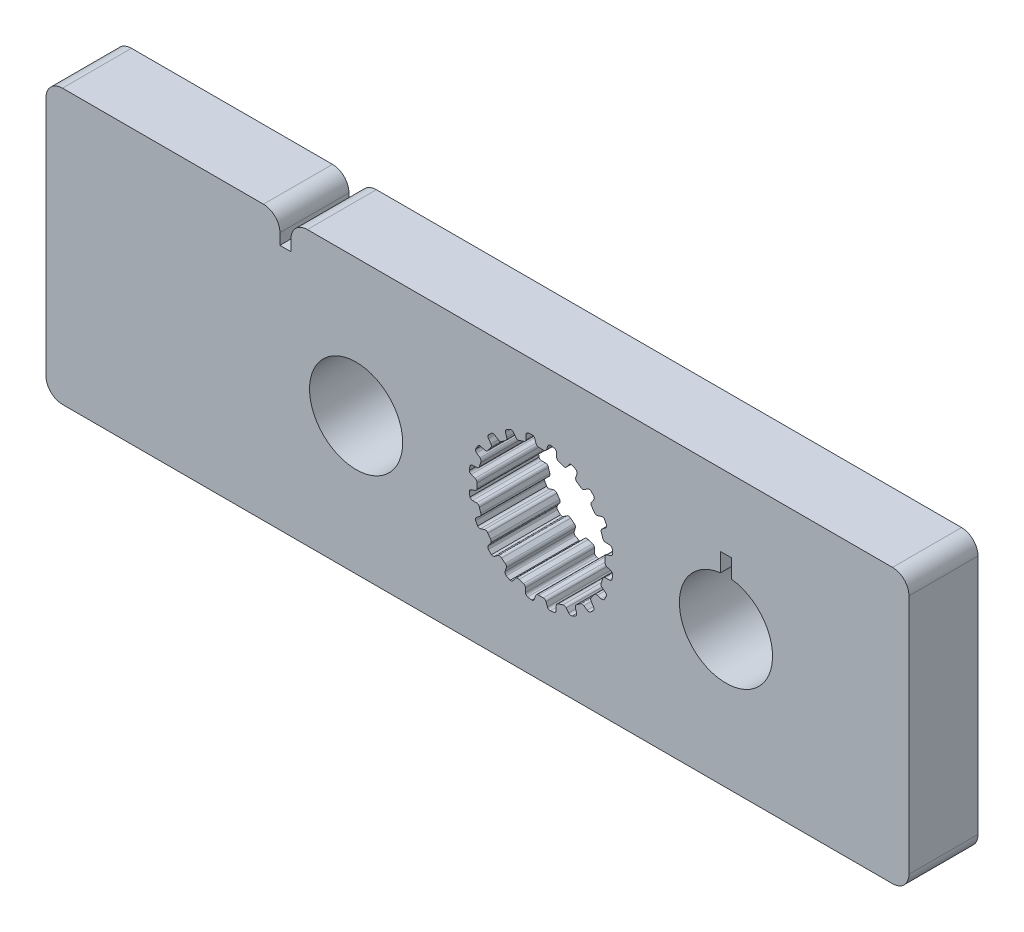
SolidWorks part; units mm, degrees
ref_plane "Front Plane" through (0, 0, 0) normal (0, 0, 1) x (1, 0, 0)
ref_plane "Top Plane" through (0, 0, 0) normal (0, 1, 0) x (1, 0, 0)
ref_plane "Right Plane" through (0, 0, 0) normal (1, 0, 0) x (0, 0, -1)
sketch "Sketch1" plane through (0, 0, 0) normal (0, 0, 1) x (1, 0, 0)
  line L0 (-0.1069, 2.9699) -> (0.1069, 2.9699)
  line L1 (0.3159, 3.2375) -> (0.2537, 3.0575)
  line L2 (-0.2964, 3.2367) -> (-0.2318, 3.0575)
  line L3 (-0.2964, 3.2367) -> (0.3159, 3.2375) construction
  line L4 (0, 3.3252) -> (0, 0) construction
  line L5 (-0.2318, 3.0575) -> (0.2537, 3.0575) construction
  line L6 (-0.4281, 3.3241) -> (0.4281, 3.3263) construction
  line L7 (0.7183, 3.1698) -> (0.7244, 2.9795)
  line L8 (0.816, 2.8576) -> (1.0195, 2.7915)
  line L9 (1.3009, 2.9815) -> (1.1862, 2.8295)
  line L10 (1.6627, 2.7927) -> (1.6097, 2.6099)
  line L11 (1.6591, 2.4655) -> (1.8322, 2.3398)
  line L12 (2.1585, 2.4335) -> (2.0025, 2.3245)
  line L13 (2.4443, 2.1423) -> (2.3374, 1.9847)
  line L14 (2.3398, 1.8322) -> (2.4655, 1.6591)
  line L15 (2.8049, 1.6474) -> (2.6228, 1.5919)
  line L16 (2.9866, 1.2821) -> (2.8363, 1.1653)
  line L17 (2.7915, 1.0195) -> (2.8576, 0.816)
  line L18 (3.1767, 0.7) -> (2.9863, 0.7035)
  line L19 (3.2367, 0.2964) -> (3.0575, 0.2318)
  line L20 (2.9699, 0.1069) -> (2.9699, -0.1069)
  line L21 (3.2375, -0.3159) -> (3.0575, -0.2537)
  line L22 (3.1698, -0.7183) -> (2.9795, -0.7244)
  line L23 (2.8576, -0.816) -> (2.7915, -1.0195)
  line L24 (2.9815, -1.3009) -> (2.8295, -1.1862)
  line L25 (2.7927, -1.6627) -> (2.6099, -1.6097)
  line L26 (2.4655, -1.6591) -> (2.3398, -1.8322)
  line L27 (2.4335, -2.1585) -> (2.3245, -2.0025)
  line L28 (2.1423, -2.4443) -> (1.9847, -2.3374)
  line L29 (1.8322, -2.3398) -> (1.6591, -2.4655)
  line L30 (1.6474, -2.8049) -> (1.5919, -2.6228)
  line L31 (1.2821, -2.9866) -> (1.1653, -2.8363)
  line L32 (1.0195, -2.7915) -> (0.816, -2.8576)
  line L33 (0.7, -3.1767) -> (0.7035, -2.9863)
  line L34 (0.2964, -3.2367) -> (0.2318, -3.0575)
  line L35 (0.1069, -2.9699) -> (-0.1069, -2.9699)
  line L36 (-0.3159, -3.2375) -> (-0.2537, -3.0575)
  line L37 (-0.7183, -3.1698) -> (-0.7244, -2.9795)
  line L38 (-0.816, -2.8576) -> (-1.0195, -2.7915)
  line L39 (-1.3009, -2.9815) -> (-1.1862, -2.8295)
  line L40 (-1.6627, -2.7927) -> (-1.6097, -2.6099)
  line L41 (-1.6591, -2.4655) -> (-1.8322, -2.3398)
  line L42 (-2.1585, -2.4335) -> (-2.0025, -2.3245)
  line L43 (-2.4443, -2.1423) -> (-2.3374, -1.9847)
  line L44 (-2.3398, -1.8322) -> (-2.4655, -1.6591)
  line L45 (-2.8049, -1.6474) -> (-2.6228, -1.5919)
  line L46 (-2.9866, -1.2821) -> (-2.8363, -1.1653)
  line L47 (-2.7915, -1.0195) -> (-2.8576, -0.816)
  line L48 (-3.1767, -0.7) -> (-2.9863, -0.7035)
  line L49 (-3.2367, -0.2964) -> (-3.0575, -0.2318)
  line L50 (-2.9699, -0.1069) -> (-2.9699, 0.1069)
  line L51 (-3.2375, 0.3159) -> (-3.0575, 0.2537)
  line L52 (-3.1698, 0.7183) -> (-2.9795, 0.7244)
  line L53 (-2.8576, 0.816) -> (-2.7915, 1.0195)
  line L54 (-2.9815, 1.3009) -> (-2.8295, 1.1862)
  line L55 (-2.7927, 1.6627) -> (-2.6099, 1.6097)
  line L56 (-2.4655, 1.6591) -> (-2.3398, 1.8322)
  line L57 (-2.4335, 2.1585) -> (-2.3245, 2.0025)
  line L58 (-2.1423, 2.4443) -> (-1.9847, 2.3374)
  line L59 (-1.8322, 2.3398) -> (-1.6591, 2.4655)
  line L60 (-1.6474, 2.8049) -> (-1.5919, 2.6228)
  line L61 (-1.2821, 2.9866) -> (-1.1653, 2.8363)
  line L62 (-1.0195, 2.7915) -> (-0.816, 2.8576)
  line L63 (-0.7, 3.1767) -> (-0.7035, 2.9863)
  line L64 (0.4281, 3.3263) -> (0.62, 3.2938)
  line L65 (1.4351, 3.0312) -> (1.6075, 2.9409)
  line L66 (2.3015, 2.4394) -> (2.4376, 2.3003)
  line L67 (2.9427, 1.6088) -> (3.0291, 1.4344)
  line L68 (3.2958, 0.6207) -> (3.3241, 0.4281)
  line L69 (3.3263, -0.4281) -> (3.2938, -0.62)
  line L70 (3.0312, -1.4351) -> (2.9409, -1.6075)
  line L71 (2.4394, -2.3015) -> (2.3003, -2.4376)
  line L72 (1.6088, -2.9427) -> (1.4344, -3.0291)
  line L73 (0.6207, -3.2958) -> (0.4281, -3.3241)
  line L74 (-0.4281, -3.3263) -> (-0.62, -3.2938)
  line L75 (-1.4351, -3.0312) -> (-1.6075, -2.9409)
  line L76 (-2.3015, -2.4394) -> (-2.4376, -2.3003)
  line L77 (-2.9427, -1.6088) -> (-3.0291, -1.4344)
  line L78 (-3.2958, -0.6207) -> (-3.3241, -0.4281)
  line L79 (-3.3263, 0.4281) -> (-3.2938, 0.62)
  line L80 (-3.0312, 1.4351) -> (-2.9409, 1.6075)
  line L81 (-2.4394, 2.3015) -> (-2.3003, 2.4376)
  line L82 (-1.6088, 2.9427) -> (-1.4344, 3.0291)
  line L83 (-0.6207, 3.2958) -> (-0.4281, 3.3241)
  line L84 (0, 0) -> (0, -6.35) construction
  line L85 (-22.9489, 6.35) -> (17.0561, 6.35)
  line L86 (-22.9489, 6.35) -> (-22.9489, -6.35)
  line L87 (-22.9489, -6.35) -> (17.0561, -6.35)
  line L88 (17.0561, 6.35) -> (17.0561, -6.35)
  line L89 (-8.5725, 0) -> (8.5725, 0) construction
  arc A0 (0.2537, 3.0575) -> (0.1069, 2.9699) centre (0.1283, 3.1009) cw
  arc A1 (-0.2318, 3.0575) -> (-0.1069, 2.9699) centre (-0.1069, 3.1026) ccw
  arc A2 (0.62, 3.2938) -> (0.7183, 3.1698) centre (0.5856, 3.1656) cw
  arc A3 (0.7244, 2.9795) -> (0.816, 2.8576) centre (0.857, 2.9838) ccw
  arc A4 (-0.4281, 3.3241) -> (-0.2964, 3.2367) centre (-0.4213, 3.1916) cw
  arc A5 (0.4281, 3.3263) -> (0.3159, 3.2375) centre (0.4413, 3.1942) ccw
  arc A6 (1.1862, 2.8295) -> (1.0195, 2.7915) centre (1.0802, 2.9095) cw
  arc A7 (1.4351, 3.0312) -> (1.3009, 2.9815) centre (1.4068, 2.9015) ccw
  arc A8 (1.6075, 2.9409) -> (1.6627, 2.7927) centre (1.5352, 2.8297) cw
  arc A9 (1.6097, 2.6099) -> (1.6591, 2.4655) centre (1.7371, 2.5729) ccw
  arc A10 (2.0025, 2.3245) -> (1.8322, 2.3398) centre (1.9264, 2.4332) cw
  arc A11 (2.3015, 2.4394) -> (2.1585, 2.4335) centre (2.2346, 2.3248) ccw
  arc A12 (2.4376, 2.3003) -> (2.4443, 2.1423) centre (2.3345, 2.2168) cw
  arc A13 (2.3374, 1.9847) -> (2.3398, 1.8322) centre (2.4472, 1.9102) ccw
  arc A14 (2.6228, 1.5919) -> (2.4655, 1.6591) centre (2.5841, 1.7189) cw
  arc A15 (2.9427, 1.6088) -> (2.8049, 1.6474) centre (2.8436, 1.5205) ccw
  arc A16 (3.0291, 1.4344) -> (2.9866, 1.2821) centre (2.9052, 1.3869) cw
  arc A17 (2.8363, 1.1653) -> (2.7915, 1.0195) centre (2.9177, 1.0605) ccw
  arc A18 (2.9863, 0.7035) -> (2.8576, 0.816) centre (2.9887, 0.8362) cw
  arc A19 (3.2958, 0.6207) -> (3.1767, 0.7) centre (3.1743, 0.5673) ccw
  arc A20 (3.3241, 0.4281) -> (3.2367, 0.2964) centre (3.1916, 0.4213) cw
  arc A21 (3.0575, 0.2318) -> (2.9699, 0.1069) centre (3.1026, 0.1069) ccw
  arc A22 (3.0575, -0.2537) -> (2.9699, -0.1069) centre (3.1009, -0.1283) cw
  arc A23 (3.3263, -0.4281) -> (3.2375, -0.3159) centre (3.1942, -0.4413) ccw
  arc A24 (3.2938, -0.62) -> (3.1698, -0.7183) centre (3.1656, -0.5856) cw
  arc A25 (2.9795, -0.7244) -> (2.8576, -0.816) centre (2.9838, -0.857) ccw
  arc A26 (2.8295, -1.1862) -> (2.7915, -1.0195) centre (2.9095, -1.0802) cw
  arc A27 (3.0312, -1.4351) -> (2.9815, -1.3009) centre (2.9015, -1.4068) ccw
  arc A28 (2.9409, -1.6075) -> (2.7927, -1.6627) centre (2.8297, -1.5352) cw
  arc A29 (2.6099, -1.6097) -> (2.4655, -1.6591) centre (2.5729, -1.7371) ccw
  arc A30 (2.3245, -2.0025) -> (2.3398, -1.8322) centre (2.4332, -1.9264) cw
  arc A31 (2.4394, -2.3015) -> (2.4335, -2.1585) centre (2.3248, -2.2346) ccw
  arc A32 (2.3003, -2.4376) -> (2.1423, -2.4443) centre (2.2168, -2.3345) cw
  arc A33 (1.9847, -2.3374) -> (1.8322, -2.3398) centre (1.9102, -2.4472) ccw
  arc A34 (1.5919, -2.6228) -> (1.6591, -2.4655) centre (1.7189, -2.5841) cw
  arc A35 (1.6088, -2.9427) -> (1.6474, -2.8049) centre (1.5205, -2.8436) ccw
  arc A36 (1.4344, -3.0291) -> (1.2821, -2.9866) centre (1.3869, -2.9052) cw
  arc A37 (1.1653, -2.8363) -> (1.0195, -2.7915) centre (1.0605, -2.9177) ccw
  arc A38 (0.7035, -2.9863) -> (0.816, -2.8576) centre (0.8362, -2.9887) cw
  arc A39 (0.6207, -3.2958) -> (0.7, -3.1767) centre (0.5673, -3.1743) ccw
  arc A40 (0.4281, -3.3241) -> (0.2964, -3.2367) centre (0.4213, -3.1916) cw
  arc A41 (0.2318, -3.0575) -> (0.1069, -2.9699) centre (0.1069, -3.1026) ccw
  arc A42 (-0.2537, -3.0575) -> (-0.1069, -2.9699) centre (-0.1283, -3.1009) cw
  arc A43 (-0.4281, -3.3263) -> (-0.3159, -3.2375) centre (-0.4413, -3.1942) ccw
  arc A44 (-0.62, -3.2938) -> (-0.7183, -3.1698) centre (-0.5856, -3.1656) cw
  arc A45 (-0.7244, -2.9795) -> (-0.816, -2.8576) centre (-0.857, -2.9838) ccw
  arc A46 (-1.1862, -2.8295) -> (-1.0195, -2.7915) centre (-1.0802, -2.9095) cw
  arc A47 (-1.4351, -3.0312) -> (-1.3009, -2.9815) centre (-1.4068, -2.9015) ccw
  arc A48 (-1.6075, -2.9409) -> (-1.6627, -2.7927) centre (-1.5352, -2.8297) cw
  arc A49 (-1.6097, -2.6099) -> (-1.6591, -2.4655) centre (-1.7371, -2.5729) ccw
  arc A50 (-2.0025, -2.3245) -> (-1.8322, -2.3398) centre (-1.9264, -2.4332) cw
  arc A51 (-2.3015, -2.4394) -> (-2.1585, -2.4335) centre (-2.2346, -2.3248) ccw
  arc A52 (-2.4376, -2.3003) -> (-2.4443, -2.1423) centre (-2.3345, -2.2168) cw
  arc A53 (-2.3374, -1.9847) -> (-2.3398, -1.8322) centre (-2.4472, -1.9102) ccw
  arc A54 (-2.6228, -1.5919) -> (-2.4655, -1.6591) centre (-2.5841, -1.7189) cw
  arc A55 (-2.9427, -1.6088) -> (-2.8049, -1.6474) centre (-2.8436, -1.5205) ccw
  arc A56 (-3.0291, -1.4344) -> (-2.9866, -1.2821) centre (-2.9052, -1.3869) cw
  arc A57 (-2.8363, -1.1653) -> (-2.7915, -1.0195) centre (-2.9177, -1.0605) ccw
  arc A58 (-2.9863, -0.7035) -> (-2.8576, -0.816) centre (-2.9887, -0.8362) cw
  arc A59 (-3.2958, -0.6207) -> (-3.1767, -0.7) centre (-3.1743, -0.5673) ccw
  arc A60 (-3.3241, -0.4281) -> (-3.2367, -0.2964) centre (-3.1916, -0.4213) cw
  arc A61 (-3.0575, -0.2318) -> (-2.9699, -0.1069) centre (-3.1026, -0.1069) ccw
  arc A62 (-3.0575, 0.2537) -> (-2.9699, 0.1069) centre (-3.1009, 0.1283) cw
  arc A63 (-3.3263, 0.4281) -> (-3.2375, 0.3159) centre (-3.1942, 0.4413) ccw
  arc A64 (-3.2938, 0.62) -> (-3.1698, 0.7183) centre (-3.1656, 0.5856) cw
  arc A65 (-2.9795, 0.7244) -> (-2.8576, 0.816) centre (-2.9838, 0.857) ccw
  arc A66 (-2.8295, 1.1862) -> (-2.7915, 1.0195) centre (-2.9095, 1.0802) cw
  arc A67 (-3.0312, 1.4351) -> (-2.9815, 1.3009) centre (-2.9015, 1.4068) ccw
  arc A68 (-2.9409, 1.6075) -> (-2.7927, 1.6627) centre (-2.8297, 1.5352) cw
  arc A69 (-2.6099, 1.6097) -> (-2.4655, 1.6591) centre (-2.5729, 1.7371) ccw
  arc A70 (-2.3245, 2.0025) -> (-2.3398, 1.8322) centre (-2.4332, 1.9264) cw
  arc A71 (-2.4394, 2.3015) -> (-2.4335, 2.1585) centre (-2.3248, 2.2346) ccw
  arc A72 (-2.3003, 2.4376) -> (-2.1423, 2.4443) centre (-2.2168, 2.3345) cw
  arc A73 (-1.9847, 2.3374) -> (-1.8322, 2.3398) centre (-1.9102, 2.4472) ccw
  arc A74 (-1.5919, 2.6228) -> (-1.6591, 2.4655) centre (-1.7189, 2.5841) cw
  arc A75 (-1.6088, 2.9427) -> (-1.6474, 2.8049) centre (-1.5205, 2.8436) ccw
  arc A76 (-1.4344, 3.0291) -> (-1.2821, 2.9866) centre (-1.3869, 2.9052) cw
  arc A77 (-1.1653, 2.8363) -> (-1.0195, 2.7915) centre (-1.0605, 2.9177) ccw
  arc A78 (-0.7035, 2.9863) -> (-0.816, 2.8576) centre (-0.8362, 2.9887) cw
  arc A79 (-0.6207, 3.2958) -> (-0.7, 3.1767) centre (-0.5673, 3.1743) ccw
  circle A80 centre (0, 0) radius 12.7 construction
  circle A81 centre (0, 0) radius 5.08 construction
  circle A82 centre (-8.5725, 0) radius 2.159
  circle A83 centre (8.5725, 0) radius 2.159
  point P14 (0, 2.9699)
  point P247 (0, 0)
  dimension "D4" = 0.1327
  dimension "D8" = 20
  dimension "D9" = 25.4
  dimension "D13" = 10.16
  dimension "D16" = 4.318
  dimension "D14" = 22.9489
  dimension "D1" = 2.9699
  dimension "D2" = 0.2139
  dimension "D3" = 0.1904
  dimension "D5" = 0.0877
  dimension "D6" = 0.4855
  dimension "D7" = 0.8563
  dimension "D10" = 12.7
  dimension "D11" = 40.005
  dimension "D12" = 6.35
  dimension "D15" = 17.145
extrude "Boss-Extrude1" add sketch "Sketch1" along normal mid plane 3.2004
sketch "Sketch2" plane through (0, 0, 1.6002) normal (0, 0, 1) x (1, 0, 0)
  line L0 (8.5725, 1.7323) -> (8.5725, 0) construction
  line L1 (17.0561, 6.35) -> (-22.9489, 6.35) construction
  line L2 (-12.105, 6.35) -> (-11.597, 6.35)
  line L3 (8.3185, 3.0023) -> (8.8265, 3.0023)
  line L4 (8.3185, 3.0023) -> (8.3185, 1.7323)
  line L5 (8.3185, 1.7323) -> (8.8265, 1.7323)
  line L6 (8.8265, 3.0023) -> (8.8265, 1.7323)
  line L7 (17.0561, -6.35) -> (17.0561, 6.35) construction
  line L8 (-12.105, 6.35) -> (-12.105, 5.08)
  line L9 (-12.105, 5.08) -> (-11.597, 5.08)
  line L10 (-11.597, 6.35) -> (-11.597, 5.08)
  circle A0 centre (8.5725, 0) radius 2.159 construction
  dimension "D1" = 0.508
  dimension "D2" = 1.27
  dimension "D3" = 1.7323
extrude "Cut-Extrude1" cut sketch "Sketch2" against normal up to surface (3.2004 mm away) up to face at (-2.9464, 0, -1.6002)
fillet "Fillet1" radius 0.762 6 edges at (17.0561, -6.35, 0) (17.0561, 6.35, 0) (-22.9489, -6.35, 0) (-22.9489, 6.35, 0) (-11.597, 6.35, 0) (-12.105, 6.35, 0)
